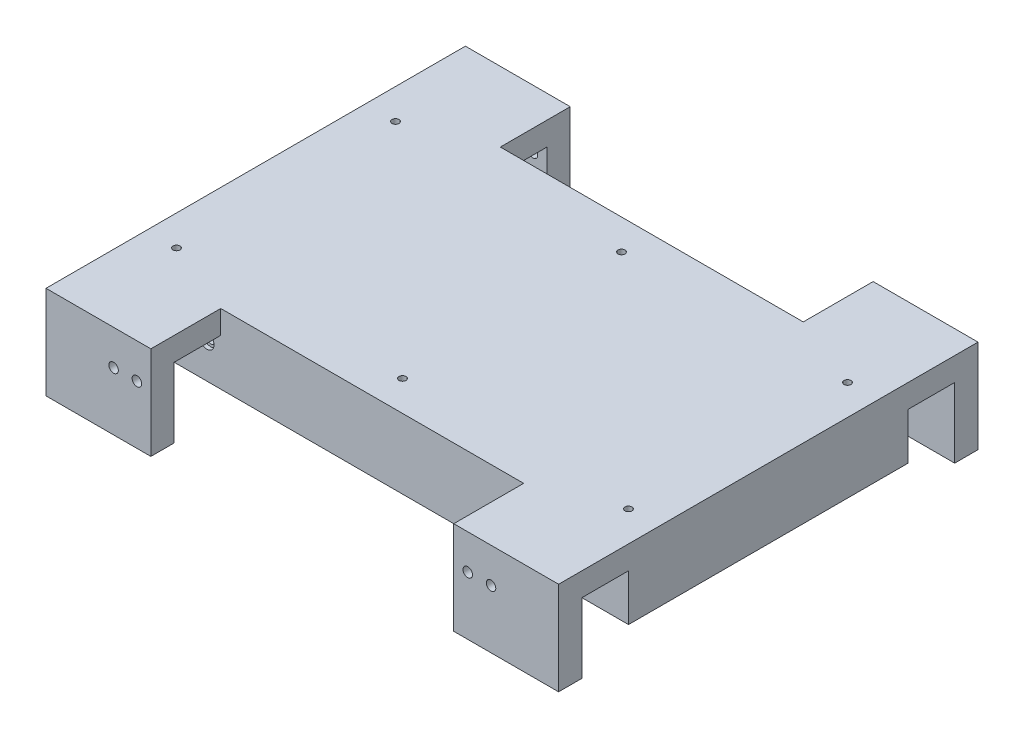
SolidWorks part; units mm, degrees
ref_plane "Front Plane" through (0, 0, 0) normal (0, 0, 1) x (1, 0, 0)
ref_plane "Top Plane" through (0, 0, 0) normal (0, 1, 0) x (1, 0, 0)
ref_plane "Right Plane" through (0, 0, 0) normal (1, 0, 0) x (0, 0, -1)
sketch "Sketch1" plane through (0, 0, 0) normal (0, 1, 0) x (1, 0, 0)
  line L1 (-80.6477, 48.697) -> (173.3523, 48.697)
  line L2 (-80.6477, 48.697) -> (-80.6477, -78.303)
  line L3 (-80.6477, -78.303) -> (173.3523, -78.303)
  line L4 (173.3523, 48.697) -> (173.3523, -78.303)
  dimension "D1" = 127
  dimension "D2" = 254
extrude "Extrude-Thin1" add sketch "Sketch1" along normal blind 50.8 thin thin type one direction wall 12.7
sketch "Sketch39" [suppressed] plane through (0, 0, 0) normal (0, -1, 0) x (1, 0, 0)
  line L0 (46.3523, -48.697) -> (46.3523, -61.397) construction
  line L1 (173.3523, -48.697) -> (-80.6477, -48.697) construction
  line L2 (186.0523, -61.397) -> (-93.3477, -61.397) construction
  line L3 (46.3523, -48.697) -> (97.1523, -48.697) construction
  line L4 (71.7523, -48.697) -> (71.7523, -61.397) construction
sketch "Sketch2" plane through (0, 50.8, 0) normal (0, 1, 0) x (1, 0, 0)
  line L1 (186.0523, -91.003) -> (-93.3477, -91.003)
  line L2 (186.0523, -91.003) -> (186.0523, 61.397)
  line L3 (186.0523, 61.397) -> (-93.3477, 61.397)
  line L4 (-93.3477, -91.003) -> (-93.3477, 61.397)
extrude "Boss-Extrude2" add sketch "Sketch2" along normal blind 6.35
sketch "Sketch13" plane through (0, 50.8, 0) normal (0, -1, 0) x (-1, 0, 0)
  line L0 (-173.3523, -14.803) -> (80.6477, -14.803) construction
  line L1 (-173.3523, -78.303) -> (-108.5823, -78.303)
  line L2 (-173.3523, -78.303) -> (-173.3523, -52.903)
  line L3 (-173.3523, -52.903) -> (-108.5823, -52.903)
  line L4 (-108.5823, -78.303) -> (-108.5823, -52.903)
  line L5 (-173.3523, -78.303) -> (-173.3523, 48.697) construction
  line L6 (80.6477, 48.697) -> (80.6477, -78.303) construction
  line L7 (-46.3523, 48.697) -> (-46.3523, -78.303) construction
  line L8 (-173.3523, 48.697) -> (80.6477, 48.697) construction
  line L9 (80.6477, -78.303) -> (-173.3523, -78.303) construction
  line L10 (-173.3523, 48.697) -> (-173.3523, 23.297)
  line L11 (-173.3523, 48.697) -> (-108.5823, 48.697)
  line L12 (-108.5823, 48.697) -> (-108.5823, 23.297)
  line L13 (-173.3523, 23.297) -> (-108.5823, 23.297)
  line L14 (80.6477, -78.303) -> (80.6477, -52.903)
  line L15 (80.6477, -52.903) -> (15.8777, -52.903)
  line L16 (15.8777, -78.303) -> (15.8777, -52.903)
  line L17 (80.6477, -78.303) -> (15.8777, -78.303)
  line L18 (80.6477, 48.697) -> (80.6477, 23.297)
  line L19 (80.6477, 48.697) -> (15.8777, 48.697)
  line L20 (15.8777, 48.697) -> (15.8777, 23.297)
  line L21 (80.6477, 23.297) -> (15.8777, 23.297)
  dimension "D1" = 64.77
  dimension "D2" = 25.4
extrude "Boss-Extrude3" add sketch "Sketch13" along normal blind 31.75
ref_plane "Plane8" [suppressed] through (71.7523, 0, 0) normal (-1, 0, 0) x (0, 0, 1)
hole_wizard "Brain Screw" positions "3DSketch6" profile "Sketch15" counterbore size "#6" standard "ANSI Inch" end condition through all
sketch3d "3DSketch6"
  line L0 (108.5823, 19.05, -48.697) -> (173.3523, 19.05, -48.697) construction
  line L1 (173.3523, 19.05, -48.697) -> (173.3523, 19.05, -23.297) construction
  point P0 (169.5423, 19.05, -44.887)
  dimension "D1" = 3.81
  dimension "D2" = 3.81
sketch "Sketch15" plane through (169.5423, 19.05, -44.887) normal (1, 0, 0) x (0, 0, -1)
  line L0 (0, 0) -> (0, 38.1)
  line L1 (0, 38.1) -> (1.8986, 38.1)
  line L3 (1.8986, 38.1) -> (1.8986, 3.5052)
  line L4 (1.8986, 3.5052) -> (3.5725, 3.5052)
  line L5 (3.5725, 3.5052) -> (3.5725, 0)
  line L7 (3.5725, 0) -> (0, 0)
  line L11 (0, -6.35) -> (0, 107.95) construction
  dimension "Thru Hole Dia." = 3.7973
  dimension "Thru Hole Depth" = 38.1
  dimension "C'Bore Dia." = 7.145
  dimension "C'Bore Depth" = 3.5052
sketch "Sketch18" plane through (0, 0, -61.397) normal (0, 0, -1) x (-1, 0, 0)
  line L1 (-186.0523, 57.15) -> (-128.9023, 57.15)
  line L2 (-186.0523, 57.15) -> (-186.0523, 6.35)
  line L3 (-186.0523, 6.35) -> (-128.9023, 6.35)
  line L4 (-128.9023, 57.15) -> (-128.9023, 6.35)
  dimension "D1" = 50.8
  dimension "D2" = 57.15
extrude "Axel Mount" add sketch "Sketch18" along normal blind 38.1 contours L4 L3 L2 L1
sketch "Sketch21" plane through (0, 0, -61.397) normal (0, 0, -1) x (-1, 0, 0)
  line L0 (-46.3523, 0) -> (-46.3523, 57.15) construction
  line L1 (-186.0523, 0) -> (93.3477, 0) construction
  line L2 (-128.9023, 57.15) -> (93.3477, 57.15) construction
ref_plane "Plane1" through (46.3523, 0, 0) normal (-1, 0, 0) x (0, 1, 0)
sketch "Sketch23" plane through (0, 57.15, 0) normal (0, 1, 0) x (1, 0, 0)
  line L0 (-93.3477, -14.803) -> (186.0523, -14.803) construction
  line L1 (-93.3477, 61.397) -> (-93.3477, -91.003) construction
  line L2 (186.0523, -91.003) -> (186.0523, 99.497) construction
ref_plane "Plane2" through (0, 0, 14.803) normal (0, 0, 1) x (1, 0, 0)
ref_plane "Plane4" through (0, 48.26, 0) normal (0, -1, 0) x (-1, 0, 0)
ref_plane "Plane6" through (173.3523, 0, 0) normal (-1, 0, 0) x (0, 0, 1)
sketch "Sketch16" plane through (0, 0, -61.397) normal (0, 0, -1) x (-1, 0, 0)
  line L2 (-45.5649, 57.15) -> (-45.5649, 0) construction
  line L4 (-69.85, 48.26) -> (69.85, 48.26) construction
  line L6 (-173.3523, -27.94) -> (-173.3523, 27.94) construction
  circle A0 centre (-161.9223, 38.1) radius 2.286
  dimension "D1" = 10.16
  dimension "D3" = 4.572
  dimension "D2" = 11.43
extrude "Axel Through" cut sketch "Sketch16" against normal up to surface (114.3 mm away)
mirror "Mirror16" about plane through (46.3523, 0, 0) normal (-1, 0, 0) of "Axel Through"
mirror "Brain Screw Mirror" about plane through (46.3523, 0, 0) normal (-1, 0, 0) of "Brain Screw"
mirror "Bran Screw Mirror 2" about plane through (0, 0, 14.803) normal (0, 0, 1) of "Brain Screw", "Brain Screw Mirror"
sketch "Sketch41" plane through (0, 50.8, 0) normal (0, -1, 0) x (1, 0, 0)
  line L0 (169.5423, -44.887) -> (-76.8377, -44.887) construction
hole_wizard "CBORE for #6 Socket Head Cap Screw2" positions "3DSketch9" profile "Sketch42" counterbore size "#6" standard "ANSI Inch" end condition through all
sketch3d "3DSketch9"
  line L2 (169.5423, 50.8, -44.887) -> (-76.8377, 50.8, -44.887) construction
  point P46 (46.3523, 50.8, -44.887)
sketch "Sketch42" plane through (46.3523, 50.8, -44.887) normal (1, 0, 0) x (0, 0, -1)
  line L0 (0, 0) -> (0, 6.35)
  line L1 (0, 6.35) -> (1.8987, 6.35)
  line L3 (1.8987, 6.35) -> (1.8986, 3.5052)
  line L4 (1.8986, 3.5052) -> (3.5725, 3.5052)
  line L5 (3.5725, 3.5052) -> (3.5725, 0)
  line L7 (3.5725, 0) -> (0, 0)
  line L11 (0, -6.35) -> (0, 107.95) construction
  dimension "Thru Hole Dia." = 3.7973
  dimension "Thru Hole Depth" = 6.35
  dimension "C'Bore Dia." = 7.145
  dimension "C'Bore Depth" = 3.5052
mirror "Mirror21" about plane through (0, 0, 14.803) normal (0, 0, 1) of "CBORE for #6 Socket Head Cap Screw2"
sketch "Sketch19" plane through (186.0523, 0, 0) normal (1, 0, 0) x (0, 0, -1)
  line L1 (61.397, 6.35) -> (86.797, 6.35)
  line L2 (61.397, 6.35) -> (61.397, 44.45)
  line L3 (61.397, 44.45) -> (86.797, 44.45)
  line L4 (86.797, 6.35) -> (86.797, 44.45)
  dimension "D1" = 25.4
  dimension "D2" = 38.1
extrude "Axel Cutout" cut sketch "Sketch19" against normal through all
mirror "Mirror17" about plane through (0, 0, 14.803) normal (0, 0, 1) of "Axel Through", "Mirror16"
mirror "Mirror1" about plane through (46.3523, 0, 0) normal (-1, 0, 0) of "Axel Cutout", "Axel Mount"
mirror "Mirror2" about plane through (0, 0, 14.803) normal (0, 0, 1) of "Axel Mount", "Axel Cutout", "Mirror1"
sketch "Sketch25" plane through (0, 0, -23.297) normal (0, 0, 1) x (1, 0, 0)
  line L1 (173.3523, 50.8) -> (122.5523, 50.8)
  line L2 (173.3523, 50.8) -> (173.3523, 25.4)
  line L3 (173.3523, 25.4) -> (122.5523, 25.4)
  line L4 (122.5523, 50.8) -> (122.5523, 25.4)
  dimension "D1" = 25.4
  dimension "D2" = 50.8
extrude "Motor Cutout" cut sketch "Sketch25" against normal blind 10.414
sketch "Sketch26" plane through (0, 0, -33.711) normal (0, 0, 1) x (1, 0, 0)
  line L0 (173.3523, 50.8) -> (122.5523, 50.8) construction
  line L1 (122.5523, 50.8) -> (122.5523, 25.4) construction
  line L2 (141.9966, 37.4582) -> (141.5459, 37.4582)
  line L3 (173.3523, 38.1) -> (122.5523, 38.1) construction
  line L4 (173.3523, 25.4) -> (173.3523, 50.8) construction
  line L5 (143.748, 37.4582) -> (143.7064, 36.0869)
  line L6 (141.9966, 38.724) -> (141.5459, 38.724)
  line L7 (141.9966, 38.724) -> (142.0382, 40.0953)
  line L8 (144.1986, 37.4582) -> (143.748, 37.4582)
  line L9 (143.7064, 36.0869) -> (141.955, 36.0869)
  line L10 (141.9966, 37.4582) -> (141.955, 36.0869)
  line L12 (143.7896, 40.0953) -> (142.0382, 40.0953)
  line L13 (143.748, 38.724) -> (143.7896, 40.0953)
  line L14 (144.1986, 38.724) -> (143.748, 38.724)
  arc A0 (144.1986, 37.4582) -> (144.1986, 38.724) centre (149.2223, 38.0911) ccw
  circle A1 centre (161.9223, 38.1) radius 2.286
  arc A2 (141.5459, 38.724) -> (141.5459, 37.4582) centre (136.5223, 38.0911) ccw
  dimension "D1" = 12.7
  dimension "D3" = 11.43
  dimension "D2" = 12.7
extrude "Motor Mount Holes" cut sketch "Sketch26" against normal blind 14.986
hole_wizard "#6 (0.204) Diameter Hole1" positions "Sketch36" profile "Sketch37" hole size "#6" standard "ANSI Inch"
sketch "Sketch36" plane through (0, 0, -48.697) normal (0, 0, 1) x (1, 0, 0)
  point P0 (149.2223, 38.0911)
  point P3 (136.5223, 38.0911)
sketch "Sketch37" plane through (149.2223, 38.0911, -48.697) normal (1, 0, 0) x (0, -1, 0)
  line L0 (0, 0) -> (0, 50.8)
  line L1 (0, 50.8) -> (2.5908, 50.8)
  line L2 (2.5908, 50.8) -> (2.5908, 0)
  line L5 (2.5908, 0) -> (0, 0)
  line L11 (0, -6.35) -> (0, 107.95) construction
  dimension "Thru Hole Dia." = 5.1816
  dimension "Thru Hole Depth" = 50.8
mirror "Mirror14" about plane through (46.3523, 0, 0) normal (-1, 0, 0) of "#6 (0.204) Diameter Hole1"
mirror "Mirror15" about plane through (0, 0, 14.803) normal (0, 0, 1) of "#6 (0.204) Diameter Hole1", "Mirror14"
mirror "Motor Cutout Mirror" about plane through (0, 0, 14.803) normal (0, 0, 1) of "Motor Cutout", "Motor Mount Holes"
mirror "Mirror6" about plane through (46.3523, 0, 0) normal (-1, 0, 0) of "Motor Cutout Mirror", "Motor Mount Holes", "Motor Cutout"
hole_wizard "CounterSinkMotor Mount" positions "3DSketch7" profile "Sketch31" counterbore size "#6" standard "ANSI Inch"
sketch3d "3DSketch7"
  line L1 (136.5223, 38.0911, -61.397) -> (136.5223, 38.0911, -48.697) construction
  line L2 (149.2223, 38.0911, -61.397) -> (149.2223, 38.0911, -48.697) construction
  point P0 (136.5223, 38.0911, -61.397)
  point P2 (149.2223, 38.0911, -61.397)
sketch "Sketch31" plane through (136.5223, 38.0911, -61.397) normal (1, 0, 0) x (0, 1, 0)
  line L0 (0, 0) -> (0, 190.5)
  line L1 (0, 190.5) -> (1.8986, 190.5)
  line L3 (1.8986, 190.5) -> (1.8987, 2.2098)
  line L4 (1.8987, 2.2098) -> (3.9687, 2.2098)
  line L5 (3.9687, 2.2098) -> (3.9687, 0)
  line L7 (3.9687, 0) -> (0, 0)
  line L11 (0, -6.35) -> (0, 107.95) construction
  dimension "Thru Hole Dia." = 3.7973
  dimension "Thru Hole Depth" = 190.5
  dimension "C'Bore Dia." = 7.9375
  dimension "C'Bore Depth" = 2.2098
mirror "Mirror9" about plane through (0, 0, 14.803) normal (0, 0, 1) of "CounterSinkMotor Mount"
mirror "Mirror10" about plane through (46.3523, 0, 0) normal (-1, 0, 0) of "CounterSinkMotor Mount", "Mirror9"
ref_plane "Plane3" through (0, 0, -74.097) normal (0, 0, -1) x (-1, 0, 0)
sketch "Sketch43" plane through (0, 0, 0) normal (0, -1, 0) x (1, 0, 0)
  line L1 (186.0523, -61.397) -> (-93.3477, -61.397)
  line L2 (186.0523, -61.397) -> (186.0523, 91.003)
  line L3 (186.0523, 91.003) -> (-93.3477, 91.003)
  line L4 (-93.3477, -61.397) -> (-93.3477, 91.003)
extrude "Cut-Extrude3" cut sketch "Sketch43" against normal up to surface (19.05 mm away) up to face at (-76.8377, 19.05, 70.9205)
sketch "Sketch44" plane through (0, 0, -86.797) normal (0, 0, 1) x (1, 0, 0)
  line L0 (-69.2177, 38.1) -> (-55.2477, 16.8868) construction
  line L1 (-64.869, 40.9639) -> (-50.899, 19.7507)
  line L3 (-73.5664, 35.2362) -> (-59.5964, 14.023)
  line L4 (-36.1977, 6.35) -> (-36.1977, 44.45) construction
  circle A0 centre (-69.2177, 38.1) radius 2.286 construction
  arc A3 (-64.869, 40.9639) -> (-73.5664, 35.2362) centre (-69.2177, 38.1) ccw
  arc A4 (-59.5964, 14.023) -> (-50.899, 19.7507) centre (-55.2477, 16.8868) ccw
  point P4 (-62.2327, 27.4934)
  point P5 (0, 0)
  dimension "D1" = 19.05
  dimension "D2" = 25.4
  dimension "D5" = 10.414
ref_plane "Plane9" through (0, 0, -74.097) normal (0, 0, -1) x (-1, 0, 0)
extrude "Axel Holes" cut sketch "Sketch44" against normal blind 5.08
mirror "Mirror29" about plane through (46.3523, 0, 0) normal (-1, 0, 0) of "Axel Holes"
mirror "Mirror30" about plane through (0, 0, 14.803) normal (0, 0, 1) of "Axel Holes", "Mirror29"
